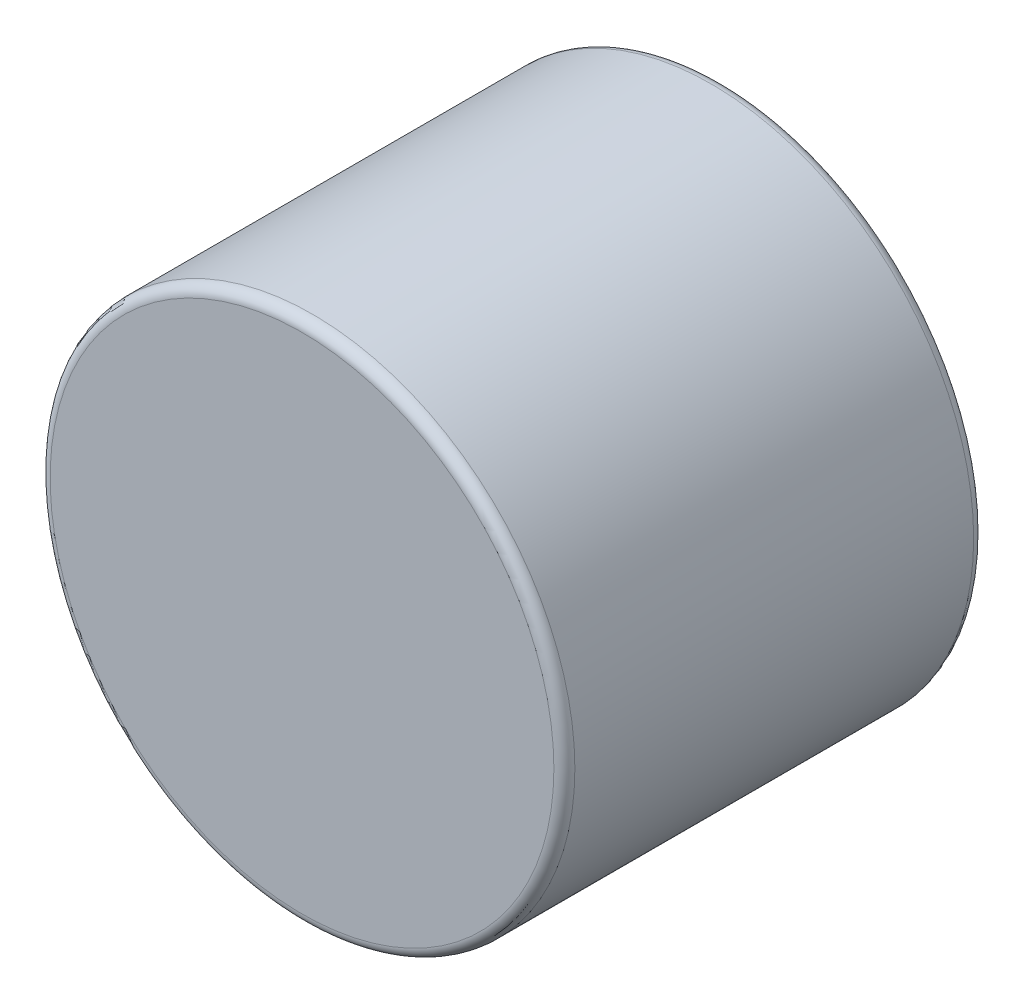
SolidWorks part; units mm, degrees
material "Plain Carbon Steel"
ref_plane "Front Plane" through (0, 0, 0) normal (0, 0, 1) x (1, 0, 0)
ref_plane "Top Plane" through (0, 0, 0) normal (0, 1, 0) x (1, 0, 0)
ref_plane "Right Plane" through (0, 0, 0) normal (1, 0, 0) x (0, 0, -1)
sketch "Sketch1" plane through (0, 0, 0) normal (0, 0, 1) x (1, 0, 0)
  circle A0 centre (0, 0) radius 3.9688 construction
  dimension "OD" = 7.9375
sketch "Sketch2" plane through (0, 0, 0) normal (1, 0, 0) x (0, 0, -1)
  line L0 (-3.175, 0) -> (3.175, 0) construction
  line L1 (0, 3.9688) -> (0, -3.9688) construction
  line L3 (-3.175, 3.9688) -> (3.175, 3.9688)
  line L4 (-3.175, 3.9688) -> (-3.175, -3.9688)
  line L5 (-3.175, -3.9688) -> (3.175, -3.9688)
  line L6 (3.175, 3.9688) -> (3.175, -3.9688)
  point P4 (0, 0)
  point P12 (0, 3.9688)
  dimension "Thickness" = 6.35
sketch "Sketch3" plane through (0, 0, 0) normal (0, 0, 1) x (1, 0, 0)
  circle A0 centre (0, 0) radius 3.9688 construction
  circle A1 centre (0, 0) radius 3.9688
extrude "Boss-Extrude1" add sketch "Sketch3" along normal up to vertex (3.175 mm away) and the other way up to vertex (3.175 mm away) up to point (0, 3.9688, 3.175) other way up to point (0, 3.9688, -3.175)
fillet "Fillet1" radius 0.1588 2 edges at (3.9688, 0, -3.175) (3.9688, 0, 3.175)
equation "\"Fillet@Fillet1\"=\"Thickness@Sketch2\"*.025"
